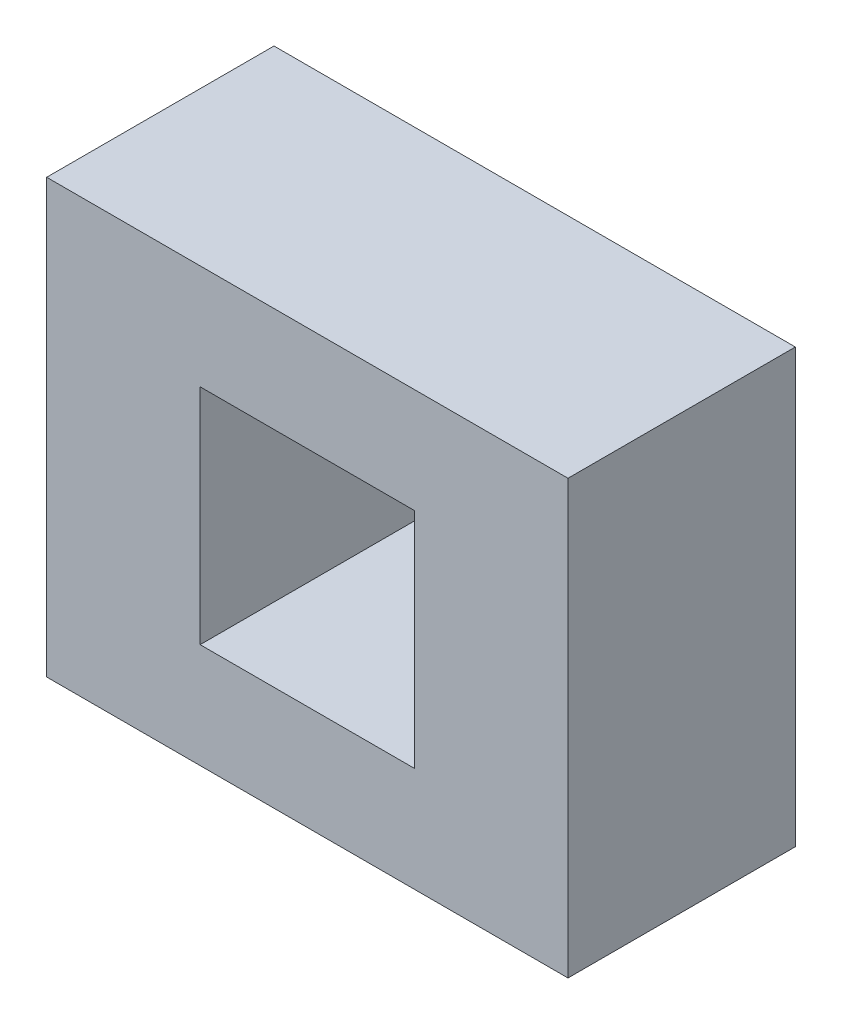
SolidWorks part; units mm, degrees
ref_plane "Front Plane" through (0, 0, 0) normal (0, 0, 1) x (1, 0, 0)
ref_plane "Top Plane" through (0, 0, 0) normal (0, 1, 0) x (1, 0, 0)
ref_plane "Right Plane" through (0, 0, 0) normal (1, 0, 0) x (0, 0, -1)
sketch "Sketch1" plane through (0, 0, 0) normal (0, 0, 1) x (1, 0, 0)
  line L1 (57.3304, -47.5967) -> (-57.3304, -47.5967)
  line L2 (57.3304, -47.5967) -> (57.3304, 47.5967)
  line L3 (57.3304, 47.5967) -> (-57.3304, 47.5967)
  line L4 (-57.3304, -47.5967) -> (-57.3304, 47.5967)
  line L5 (57.3304, -47.5967) -> (-57.3304, 47.5967) construction
  line L6 (57.3304, 47.5967) -> (-57.3304, -47.5967) construction
  line L7 (23.5751, -24.5574) -> (-23.5751, -24.5574)
  line L8 (23.5751, -24.5574) -> (23.5751, 24.5574)
  line L9 (23.5751, 24.5574) -> (-23.5751, 24.5574)
  line L10 (-23.5751, -24.5574) -> (-23.5751, 24.5574)
  line L11 (23.5751, -24.5574) -> (-23.5751, 24.5574) construction
  line L12 (23.5751, 24.5574) -> (-23.5751, -24.5574) construction
  point P0 (0, 0)
  point P6 (0, 0)
extrude "Boss-Extrude1" add sketch "Sketch1" along normal blind 50
